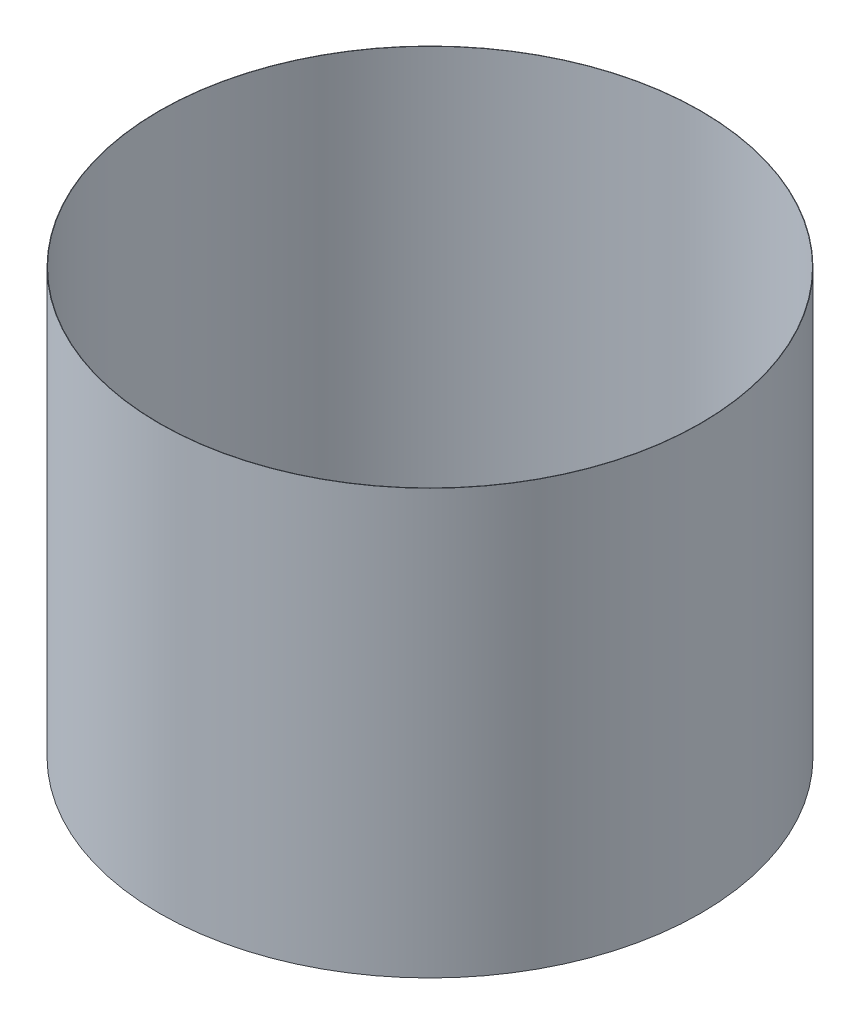
SolidWorks part; units mm, degrees
ref_plane "前视基准面" through (0, 0, 0) normal (0, 0, 1) x (1, 0, 0)
ref_plane "上视基准面" through (0, 0, 0) normal (0, 1, 0) x (1, 0, 0)
ref_plane "右视基准面" through (0, 0, 0) normal (1, 0, 0) x (0, 0, -1)
sketch "草图1" plane through (0, 0, 0) normal (0, 1, 0) x (1, 0, 0)
  circle A0 centre (0, 0) radius 255.1218
  circle A1 centre (0, 0) radius 255.4218
  dimension "D1" = 510.2437
  dimension "D2" = 0.3
extrude "凸台-拉伸1" add sketch "草图1" along normal blind 400
